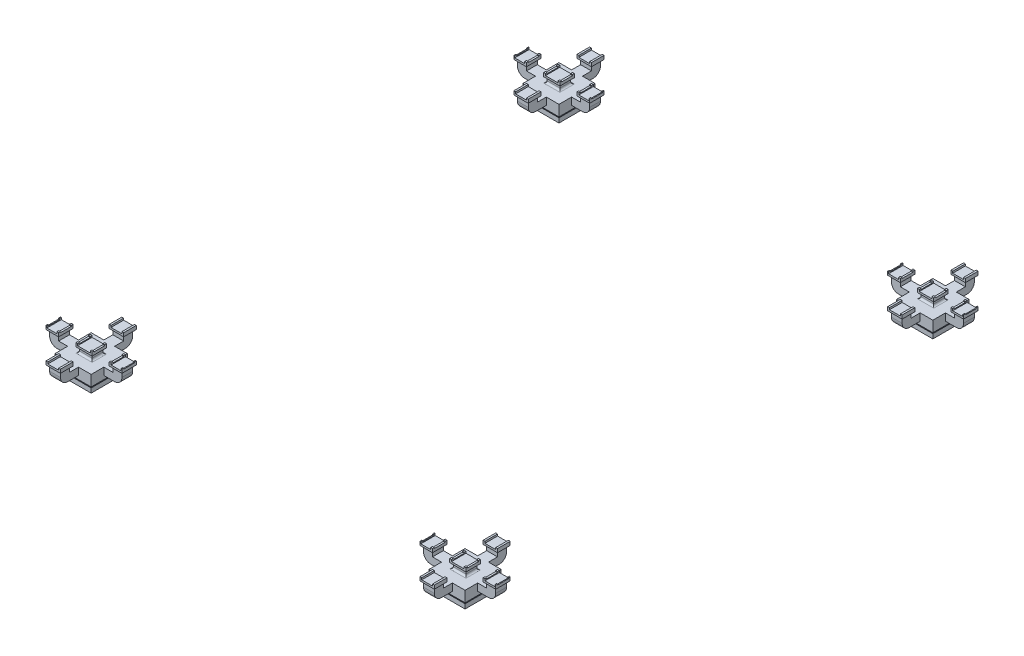
SolidWorks part; units mm, degrees
material "松木"
ref_plane "前视基准面" through (0, 0, 0) normal (0, 0, 1) x (1, 0, 0)
ref_plane "上视基准面" through (0, 0, 0) normal (0, 1, 0) x (1, 0, 0)
ref_plane "右视基准面" through (0, 0, 0) normal (1, 0, 0) x (0, 0, -1)
sketch "草图1" plane through (0, 0, 0) normal (0, 1, 0) x (1, 0, 0)
  line L1 (0, 0) -> (50, 0)
  line L2 (0, 0) -> (0, 50)
  line L3 (0, 50) -> (50, 50)
  line L4 (50, 0) -> (50, 50)
  dimension "D1" = 50
  dimension "D2" = 50
extrude "凸台-拉伸1" add sketch "草图1" along normal blind 70
sketch "草图2" plane through (0, 70, 0) normal (0, 1, 0) x (1, 0, 0)
  line L0 (-50, -50) -> (-50, 100)
  line L1 (0, 0) -> (50, 0)
  line L2 (0, 0) -> (0, 50)
  line L3 (0, 50) -> (50, 50)
  line L4 (50, 0) -> (50, 50)
  line L5 (-50, 100) -> (100, 100)
  line L6 (100, -50) -> (100, 100)
  line L7 (-50, -50) -> (100, -50)
  dimension "D1" = 50
ref_plane "基准面4" through (0, 70, 0) normal (0, 1, 0) x (1, 0, 0)
ref_plane "基准面5" through (0, 100, 0) normal (0, 1, 0) x (1, 0, 0)
sketch "草图3" plane through (0, 100, 0) normal (0, 1, 0) x (1, 0, 0)
  line L0 (-75, -75) -> (-75, 125)
  line L1 (-50, -50) -> (100, -50)
  line L2 (-50, -50) -> (-50, 100)
  line L3 (-50, 100) -> (100, 100)
  line L4 (100, -50) -> (100, 100)
  line L5 (-75, 125) -> (125, 125)
  line L6 (125, -75) -> (125, 125)
  line L7 (-75, -75) -> (125, -75)
  dimension "D1" = 25
loft "放样2" add section "草图2" section "草图3"
sketch "草图4" plane through (0, 100, 0) normal (0, 1, 0) x (1, 0, 0)
  line L1 (125, -75) -> (-75, -75)
  line L2 (125, -75) -> (125, 125)
  line L3 (125, 125) -> (-75, 125)
  line L4 (-75, -75) -> (-75, 125)
extrude "凸台-拉伸2" add sketch "草图4" along normal blind 20
sketch "草图5" plane through (0, 120, 0) normal (0, 1, 0) x (1, 0, 0)
  line L1 (-75, -75) -> (-5, -75)
  line L2 (-75, -75) -> (-75, -5)
  line L3 (-75, -5) -> (-5, -5)
  line L4 (-5, -75) -> (-5, -5)
  line L5 (125, -75) -> (55, -75)
  line L6 (125, -75) -> (125, -5)
  line L7 (125, -5) -> (55, -5)
  line L8 (55, -75) -> (55, -5)
  line L9 (125, 125) -> (55, 125)
  line L10 (125, 125) -> (125, 55)
  line L11 (125, 55) -> (55, 55)
  line L12 (55, 125) -> (55, 55)
  line L13 (-75, 125) -> (-5, 125)
  line L14 (-75, 125) -> (-75, 55)
  line L15 (-75, 55) -> (-5, 55)
  line L16 (-5, 125) -> (-5, 55)
  dimension "D1" = 70
  dimension "D2" = 70
extrude "凸台-拉伸3" add sketch "草图5" along normal blind 40
sketch "草图6" plane through (0, 120, 0) normal (0, 1, 0) x (1, 0, 0)
  line L0 (-75, 55) -> (-5, 55) construction
  line L1 (-175, -5) -> (225, -5)
  line L2 (-175, -5) -> (-175, 55)
  line L3 (-175, 55) -> (225, 55)
  line L4 (225, -5) -> (225, 55)
  line L5 (-5, -5) -> (-75, -5) construction
  line L7 (55, 125) -> (-5, 125) construction
  point P10 (25, 55)
  point P13 (25, 125)
  dimension "D1" = 400
extrude "凸台-拉伸4" add sketch "草图6" along normal blind 40
sketch "草图7" plane through (0, 160, 0) normal (0, 1, 0) x (1, 0, 0)
  line L0 (225, 55) -> (125, 55) construction
  line L1 (225, -5) -> (175, -5)
  line L2 (225, -5) -> (225, 55)
  line L3 (225, 55) -> (175, 55)
  line L4 (175, -5) -> (175, 55)
  line L5 (-75, 55) -> (-175, 55) construction
  line L6 (-175, -5) -> (-125, -5)
  line L7 (-175, -5) -> (-175, 55)
  line L8 (-175, 55) -> (-125, 55)
  line L9 (-125, -5) -> (-125, 55)
  line L10 (125, 55) -> (125, 125) construction
  line L11 (55, -5) -> (125, -5)
  line L12 (55, -5) -> (55, 55)
  line L13 (55, 55) -> (125, 55)
  line L14 (125, -5) -> (125, 55)
  line L16 (-5, -5) -> (-75, -5)
  line L17 (-5, -5) -> (-5, 55)
  line L18 (-5, 55) -> (-75, 55)
  line L19 (-75, -5) -> (-75, 55)
extrude "凸台-拉伸6" add sketch "草图7" along normal blind 20
sketch "草图8" plane through (0, 180, 0) normal (0, 1, 0) x (1, 0, 0)
  line L0 (-75, -5) -> (-5, -5) construction
  line L1 (-75, 55) -> (-10, 55)
  line L2 (-75, 55) -> (-75, -5)
  line L3 (-75, -5) -> (-10, -5)
  line L4 (-10, 55) -> (-10, -5)
  line L5 (55, -5) -> (125, -5) construction
  line L6 (125, 55) -> (60, 55)
  line L7 (125, 55) -> (125, -5)
  line L8 (125, -5) -> (60, -5)
  line L9 (60, 55) -> (60, -5)
  line L10 (-5, -5) -> (-5, 55) construction
  line L11 (55, 55) -> (55, -5) construction
  dimension "D1" = 5
  dimension "D2" = 5
extrude "切除-拉伸1" cut sketch "草图8" against normal blind 20
fillet "圆角1" radius 40 2 edges at (-175, 120, -25) (225, 120, -25)
ref_plane "基准面6" through (0, 180, 0) normal (0, 1, 0) x (1, 0, 0)
ref_plane "基准面7" through (0, 190, 0) normal (0, 1, 0) x (1, 0, 0)
sketch "草图9" plane through (0, 190, 0) normal (0, 1, 0) x (1, 0, 0)
  line L0 (235, 65) -> (235, -15)
  line L1 (225, 55) -> (175, 55)
  line L2 (225, 55) -> (225, -5)
  line L3 (225, -5) -> (175, -5)
  line L4 (175, 55) -> (175, -5)
  line L5 (-175, 55) -> (-125, 55)
  line L6 (-175, 55) -> (-175, -5)
  line L7 (-175, -5) -> (-125, -5)
  line L8 (-125, 55) -> (-125, -5)
  line L9 (235, -15) -> (165, -15)
  line L10 (165, 65) -> (165, -15)
  line L11 (235, 65) -> (165, 65)
  line L12 (-185, 65) -> (-185, -15)
  line L13 (-185, -15) -> (-115, -15)
  line L14 (-115, 65) -> (-115, -15)
  line L15 (-185, 65) -> (-115, 65)
  dimension "D1" = 10
  dimension "D2" = 10
sketch "草图10" plane through (0, 180, 0) normal (0, 1, 0) x (1, 0, 0)
  line L1 (225, 55) -> (175, 55)
  line L2 (225, 55) -> (225, -5)
  line L3 (225, -5) -> (175, -5)
  line L4 (175, 55) -> (175, -5)
  line L5 (-125, 55) -> (-175, 55)
  line L6 (-125, 55) -> (-125, -5)
  line L7 (-125, -5) -> (-175, -5)
  line L8 (-175, 55) -> (-175, -5)
loft "放样3" add section "草图10" section "草图9"
ref_plane "基准面8" through (25, 0, 0) normal (1, 0, 0) x (0, 0, -1)
sketch "草图12" plane through (0, 190, 0) normal (0, 1, 0) x (1, 0, 0)
  line L1 (165, -15) -> (235, -15)
  line L2 (165, -15) -> (165, 65)
  line L3 (165, 65) -> (235, 65)
  line L4 (235, -15) -> (235, 65)
extrude "凸台-拉伸7" add sketch "草图12" along normal blind 10
sketch "草图13" plane through (0, 200, 0) normal (0, 1, 0) x (1, 0, 0)
  line L0 (235, 65) -> (165, 65) construction
  line L1 (165, -15) -> (175, -15)
  line L2 (165, -15) -> (165, 65)
  line L3 (165, 65) -> (175, 65)
  line L4 (175, -15) -> (175, 65)
  line L6 (235, -15) -> (230, -15)
  line L7 (235, -15) -> (235, 65)
  line L8 (235, 65) -> (230, 65)
  line L9 (230, -15) -> (230, 65)
  dimension "D1" = 10
  dimension "D2" = 5
extrude "凸台-拉伸8" add sketch "草图13" along normal blind 10
mirror "镜向2" about plane through (25, 0, 0) normal (1, 0, 0) of "放样3", "凸台-拉伸7", "凸台-拉伸8"
sketch "草图15" plane through (0, 120, 0) normal (0, 1, 0) x (1, 0, 0)
  line L0 (55, 125) -> (55, 55) construction
  line L1 (55, 225) -> (-5, 225)
  line L2 (55, 225) -> (55, -175)
  line L3 (55, -175) -> (-5, -175)
  line L4 (-5, 225) -> (-5, -175)
  line L5 (-5, 55) -> (-5, 125) construction
  line L6 (-5, -5) -> (-5, 55) construction
  point P8 (-5, 25)
  point P11 (-5, 25)
  dimension "D1" = 400
extrude "凸台-拉伸9" add sketch "草图15" along normal blind 40
sketch "草图16" plane through (0, 160, 0) normal (0, 1, 0) x (1, 0, 0)
  line L0 (-5, -75) -> (-5, -175) construction
  line L1 (55, -175) -> (-5, -175)
  line L2 (55, -175) -> (55, -125)
  line L3 (55, -125) -> (-5, -125)
  line L4 (-5, -175) -> (-5, -125)
  line L5 (55, 125) -> (55, 225) construction
  line L6 (-5, 225) -> (55, 225)
  line L7 (-5, 225) -> (-5, 175)
  line L8 (-5, 175) -> (55, 175)
  line L9 (55, 225) -> (55, 175)
extrude "凸台-拉伸10" add sketch "草图16" along normal blind 20
sketch "草图17" plane through (0, 180, 0) normal (0, 1, 0) x (1, 0, 0)
  line L1 (55, -175) -> (-5, -175)
  line L2 (55, -175) -> (55, -125)
  line L3 (55, -125) -> (-5, -125)
  line L4 (-5, -175) -> (-5, -125)
  line L5 (55, 225) -> (-5, 225)
  line L6 (55, 225) -> (55, 175)
  line L7 (55, 175) -> (-5, 175)
  line L8 (-5, 225) -> (-5, 175)
sketch "草图18" plane through (0, 190, 0) normal (0, 1, 0) x (1, 0, 0)
  line L0 (65, -185) -> (65, -115)
  line L1 (55, -175) -> (-5, -175)
  line L2 (55, -175) -> (55, -125)
  line L3 (55, -125) -> (-5, -125)
  line L4 (-5, -175) -> (-5, -125)
  line L9 (65, -115) -> (-15, -115)
  line L10 (-15, -185) -> (-15, -115)
  line L11 (65, -185) -> (-15, -185)
  dimension "D1" = 10
loft "放样4" add section "草图18" section "草图17"
ref_plane "基准面10" through (0, 0, -25) normal (0, 0, 1) x (1, 0, 0)
sketch "草图19" plane through (0, 190, 0) normal (0, 1, 0) x (1, 0, 0)
  line L12 (-15, -185) -> (65, -185)
  line L13 (-15, -185) -> (-15, -115)
  line L14 (-15, -115) -> (65, -115)
  line L15 (65, -185) -> (65, -115)
extrude "凸台-拉伸12" add sketch "草图19" along normal blind 10
sketch "草图20" plane through (0, 200, 0) normal (0, 1, 0) x (1, 0, 0)
  line L0 (-15, -185) -> (65, -185) construction
  line L1 (-15, -115) -> (-5, -115)
  line L2 (-15, -115) -> (-15, -185)
  line L3 (-15, -185) -> (-5, -185)
  line L4 (-5, -115) -> (-5, -185)
  line L6 (65, -115) -> (55, -115)
  line L7 (65, -115) -> (65, -185)
  line L8 (65, -185) -> (55, -185)
  line L9 (55, -115) -> (55, -185)
  dimension "D1" = 10
  dimension "D2" = 10
extrude "凸台-拉伸13" add sketch "草图20" along normal blind 10
mirror "镜向3" about plane through (0, 0, -25) normal (0, 0, 1) of "放样4", "凸台-拉伸12", "凸台-拉伸13"
fillet "圆角3" radius 10 2 edges at (60, 160, -25) (-10, 160, -25)
sketch "草图21" plane through (0, 160, 0) normal (0, 1, 0) x (1, 0, 0)
  line L1 (-5, -5) -> (55, -5)
  line L2 (-5, -5) -> (-5, 55)
  line L3 (-5, 55) -> (55, 55)
  line L4 (55, -5) -> (55, 55)
extrude "凸台-拉伸14" add sketch "草图21" along normal blind 20
fillet "圆角4" radius 10 2 edges at (25, 160, -55) (25, 160, 5)
sketch "草图22" plane through (0, 180, 0) normal (0, 1, 0) x (1, 0, 0)
  line L1 (-10, -5) -> (60, -5)
  line L2 (-10, -5) -> (-10, 55)
  line L3 (-10, 55) -> (60, 55)
  line L4 (60, -5) -> (60, 55)
sketch "草图23" plane through (0, 190, 0) normal (0, 1, 0) x (1, 0, 0)
  line L0 (-20, -15) -> (-20, 65)
  line L1 (-10, -5) -> (60, -5)
  line L2 (-10, -5) -> (-10, 55)
  line L3 (-10, 55) -> (60, 55)
  line L4 (60, -5) -> (60, 55)
  line L5 (-20, 65) -> (70, 65)
  line L6 (70, -15) -> (70, 65)
  line L7 (-20, -15) -> (70, -15)
  dimension "D1" = 10
loft "放样5" add profiles "草图22" section "草图22" section "草图23"
sketch "草图24" plane through (0, 190, 0) normal (0, 1, 0) x (1, 0, 0)
  line L0 (-20, 65) -> (70, 65) construction
  line L1 (-20, -15) -> (-10, -15)
  line L2 (-20, -15) -> (-20, 65)
  line L3 (-20, 65) -> (-10, 65)
  line L5 (-20, -15) -> (70, -15) construction
  line L6 (70, 65) -> (60, 65)
  line L7 (70, 65) -> (70, -15)
  line L8 (70, -15) -> (60, -15)
  line L11 (-20, -15) -> (70, -15)
  line L12 (-20, -15) -> (-20, 65)
  line L13 (-20, 65) -> (70, 65)
  line L14 (70, -15) -> (70, 65)
  dimension "D1" = 10
  dimension "D2" = 10
extrude "凸台-拉伸15" add sketch "草图24" along normal blind 10
sketch "草图25" plane through (0, 200, 0) normal (0, 1, 0) x (1, 0, 0)
  line L0 (70, 65) -> (-20, 65) construction
  line L1 (-20, -15) -> (-10, -15)
  line L2 (-20, -15) -> (-20, 65)
  line L3 (-20, 65) -> (-10, 65)
  line L4 (-10, -15) -> (-10, 65)
  line L5 (-20, -15) -> (70, -15) construction
  line L6 (70, 65) -> (60, 65)
  line L7 (70, 65) -> (70, -15)
  line L8 (70, -15) -> (60, -15)
  line L9 (60, 65) -> (60, -15)
  dimension "D1" = 10
  dimension "D2" = 10
extrude "凸台-拉伸16" add sketch "草图25" along normal blind 10
sketch "草图26" plane through (0, 210, 0) normal (0, 1, 0) x (1, 0, 0)
  line L0 (230, -15) -> (235, -15) construction
  line L1 (235, -5) -> (-185, -5)
  line L2 (235, -5) -> (235, 55)
  line L3 (235, 55) -> (-185, 55)
  line L4 (-185, -5) -> (-185, 55)
  line L5 (235, 65) -> (230, 65) construction
  line L6 (-185, -15) -> (-185, 65) construction
  line L7 (235, -15) -> (235, 65) construction
  dimension "D1" = 10
  dimension "D2" = 10
extrude "切除-拉伸2" cut sketch "草图26" against normal blind 5
fillet "圆角5" radius 40 2 edges at (25, 120, -225) (25, 120, 175)
scale "缩放比例1" scale about origin uniform scaling yes scale factor 2
sketch "草图30" plane through (0, 0, 0) normal (0, -1, 0) x (1, 0, 0)
  line L1 (100, 0) -> (0, 0)
  line L2 (100, 0) -> (100, -100)
  line L3 (100, -100) -> (0, -100)
  line L4 (0, 0) -> (0, -100)
  line L8 (90, -10) -> (90, -90)
  line L9 (90, -90) -> (10, -90)
  line L10 (10, -10) -> (10, -90)
  line L11 (90, -10) -> (10, -10)
  dimension "D1" = 10
extrude "切除-拉伸4" cut sketch "草图30" against normal blind 140
sketch "草图31" plane through (0, 0, 0) normal (0, -1, 0) x (1, 0, 0)
  line L1 (10, -10) -> (90, -10)
  line L2 (10, -10) -> (10, -90)
  line L3 (10, -90) -> (90, -90)
  line L4 (90, -10) -> (90, -90)
extrude "凸台-拉伸18" add sketch "草图31" along normal blind 10
sketch "草图32" plane through (0, 140, 0) normal (0, -1, 0) x (1, 0, 0)
  line L1 (-100, -200) -> (200, -200)
  line L2 (-100, -200) -> (-100, 100)
  line L3 (-100, 100) -> (200, 100)
  line L4 (200, -200) -> (200, 100)
  line L5 (10, -90) -> (90, -90)
  line L6 (10, -90) -> (10, -10)
  line L7 (10, -10) -> (90, -10)
  line L8 (90, -90) -> (90, -10)
extrude "凸台-拉伸19" add sketch "草图32" along normal blind 50
pattern_linear "阵列(线性)1" count 2 spacing 5180 along (0, 0, -1) count 2 spacing 4140 along (1, 0, 0) of bodies 141 136
